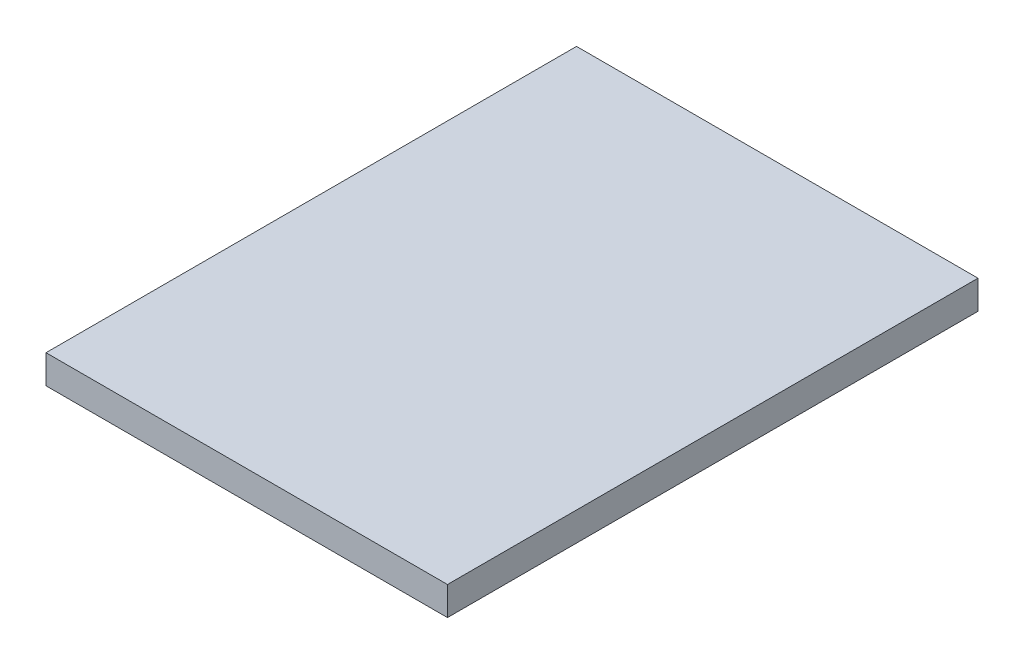
SolidWorks part; units mm, degrees
material "Mahogany"
ref_plane "Front Plane" through (0, 0, 0) normal (0, 0, 1) x (1, 0, 0)
ref_plane "Top Plane" through (0, 0, 0) normal (0, 1, 0) x (1, 0, 0)
ref_plane "Right Plane" through (0, 0, 0) normal (1, 0, 0) x (0, 0, -1)
sketch "Sketch1" plane through (0, 0, 0) normal (0, 1, 0) x (1, 0, 0)
  line L1 (112, -148) -> (-112, -148)
  line L2 (112, -148) -> (112, 148)
  line L3 (112, 148) -> (-112, 148)
  line L4 (-112, -148) -> (-112, 148)
  line L5 (112, -148) -> (-112, 148) construction
  line L6 (112, 148) -> (-112, -148) construction
  point P0 (0, 0)
  dimension "D1" = 224
  dimension "D2" = 296
extrude "Boss-Extrude1" add sketch "Sketch1" along normal blind 16
